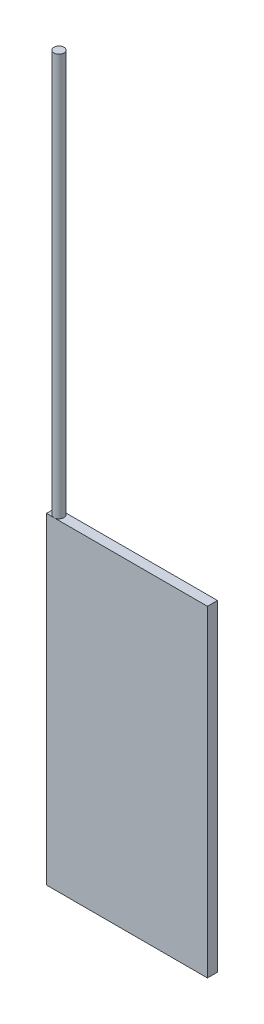
SolidWorks part; units mm, degrees
material "1060 Alloy"
ref_plane "Front Plane" through (0, 0, 0) normal (0, 0, 1) x (1, 0, 0)
ref_plane "Top Plane" through (0, 0, 0) normal (0, 1, 0) x (1, 0, 0)
ref_plane "Right Plane" through (0, 0, 0) normal (1, 0, 0) x (0, 0, -1)
sketch "Sketch1" plane through (0, 0, 0) normal (0, 0, 1) x (1, 0, 0)
  line L1 (0, 0) -> (50.8, 0)
  line L2 (0, 0) -> (0, 101.6)
  line L3 (0, 101.6) -> (50.8, 101.6)
  line L4 (50.8, 0) -> (50.8, 101.6)
  dimension "D1" = 101.6
  dimension "D2" = 50.8
extrude "Boss-Extrude1" add sketch "Sketch1" along normal blind 3.175
sketch "Sketch2" plane through (0, 101.6, 0) normal (0, 1, 0) x (1, 0, 0)
  line L0 (0, -1.5875) -> (2.3392, -1.5875) construction
  line L1 (0, -3.175) -> (0, 0) construction
  circle A0 centre (2.3392, -1.5875) radius 1.5875
  dimension "D1" = 3.175
extrude "Boss-Extrude2" add sketch "Sketch2" along normal blind 127
